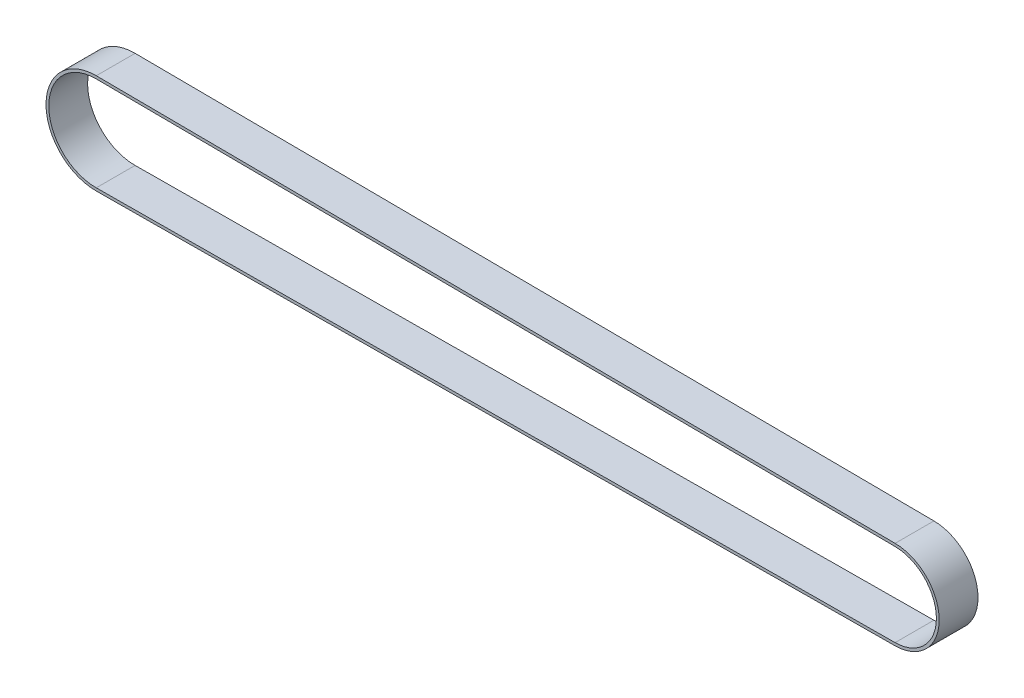
SolidWorks part; units mm, degrees
ref_plane "Front Plane" through (0, 0, 0) normal (0, 0, 1) x (1, 0, 0)
ref_plane "Top Plane" through (0, 0, 0) normal (0, 1, 0) x (1, 0, 0)
ref_plane "Right Plane" through (0, 0, 0) normal (1, 0, 0) x (0, 0, -1)
sketch "Sketch2" plane through (0, 0, 0) normal (0, 0, 1) x (1, 0, 0)
  line L0 (0, 0) -> (1, 0) construction
  line L1 (0, 0) -> (0, 1) construction
  line L4 (147.0521, -6.9998) -> (3.059, -7.9998)
  line L5 (3.059, 8.9998) -> (147.0521, 7.9998)
  arc A1 (147.0521, 7.9998) -> (147.0521, -6.9998) centre (147, 0.5) cw
  arc A2 (3.059, -7.9998) -> (3.059, 8.9998) centre (3, 0.5) cw
extrude "Extrude-Thin1" add sketch "Sketch2" against normal blind 7 thin thin type one direction wall 0.5
